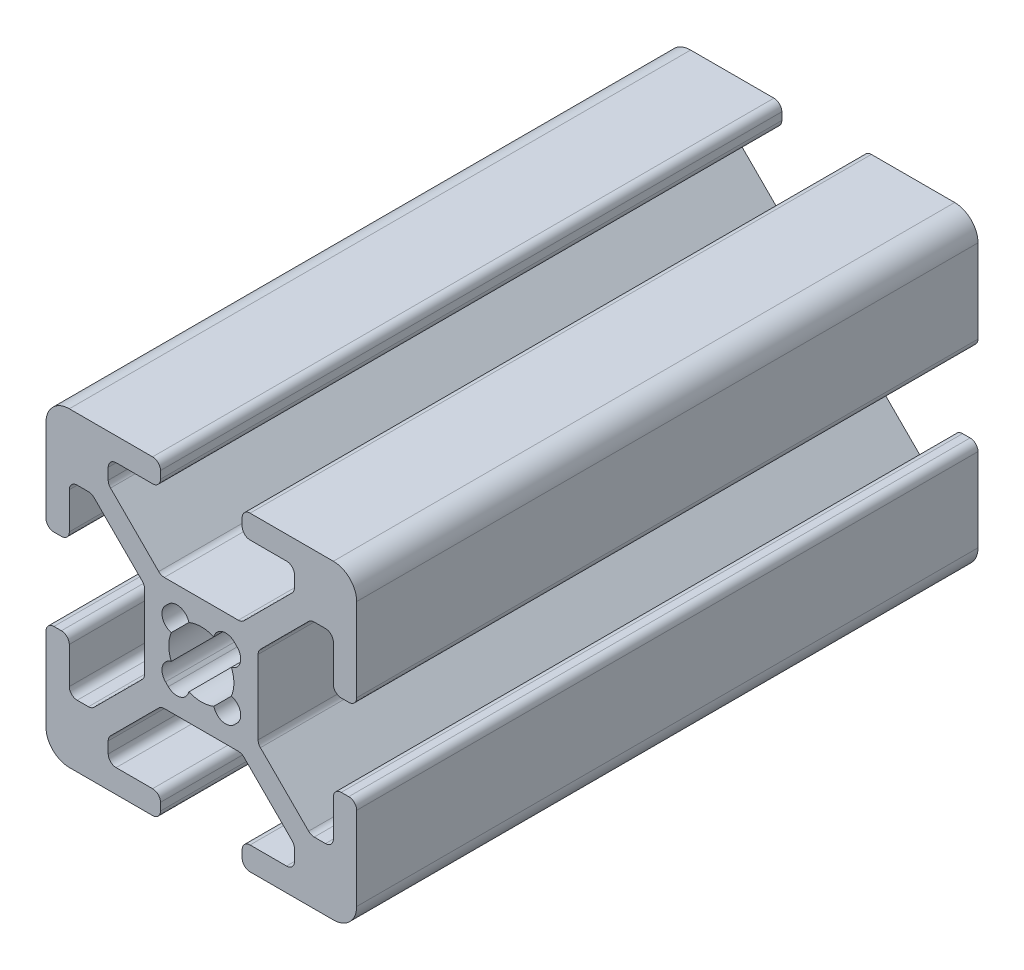
SolidWorks part; units mm, degrees
ref_plane "Front Plane" through (0, 0, 0) normal (0, 0, 1) x (1, 0, 0)
ref_plane "Top Plane" through (0, 0, 0) normal (0, 1, 0) x (1, 0, 0)
ref_plane "Right Plane" through (0, 0, 0) normal (1, 0, 0) x (0, 0, -1)
sketch "Sketch1" plane through (0, 0, 0) normal (0, 0, 1) x (1, 0, 0)
  line L0 (-5.0323, -0.3411) -> (-5.5163, -0.3411)
  line L1 (-6.0243, 0.1669) -> (-6.0243, 2.5159)
  line L2 (-4.5243, 0.1669) -> (-4.5243, 5.5289)
  line L3 (-10.8693, -5.355) -> (-10.8693, -0.5871)
  line L4 (-7.2582, 3.0239) -> (-6.5323, 3.0239)
  line L5 (-7.6174, 2.8752) -> (-10.7205, -0.2279)
  line L6 (-5.0323, -5.6011) -> (-5.5163, -5.6011)
  line L7 (-4.5243, -6.1091) -> (-4.5243, -11.4711)
  line L8 (-6.0243, -6.1091) -> (-6.0243, -8.4581)
  line L9 (-7.2582, -8.9661) -> (-6.5323, -8.9661)
  line L10 (-7.6174, -8.8173) -> (-10.7205, -5.7142)
  line L11 (-12.3994, -5.2756) -> (-12.2198, -5.096)
  line L12 (-17.1543, 6.5209) -> (-17.1543, 6.0369)
  line L13 (-17.6623, 7.0289) -> (-23.0243, 7.0289)
  line L14 (-17.6623, 5.5289) -> (-20.0113, 5.5289)
  line L15 (-12.1404, 0.6839) -> (-16.9082, 0.6839)
  line L16 (-20.5193, 4.295) -> (-20.5193, 5.0209)
  line L17 (-20.3705, 3.9358) -> (-17.2674, 0.8327)
  line L18 (-11.8943, 6.5209) -> (-11.8943, 6.0369)
  line L19 (-11.3863, 7.0289) -> (-6.0243, 7.0289)
  line L20 (-11.3863, 5.5289) -> (-9.0373, 5.5289)
  line L21 (-8.5293, 4.295) -> (-8.5293, 5.0209)
  line L22 (-8.6781, 3.9358) -> (-11.7812, 0.8327)
  line L23 (-12.2198, -0.8462) -> (-12.3994, -0.6666)
  line L24 (-24.0163, -5.6011) -> (-23.5323, -5.6011)
  line L25 (-24.5243, -6.1091) -> (-24.5243, -11.4711)
  line L26 (-23.0243, -6.1091) -> (-23.0243, -8.4581)
  line L27 (-18.1793, -0.5871) -> (-18.1793, -5.355)
  line L28 (-21.7904, -8.9661) -> (-22.5163, -8.9661)
  line L29 (-21.4312, -8.8173) -> (-18.3281, -5.7142)
  line L30 (-24.0163, -0.3411) -> (-23.5323, -0.3411)
  line L31 (-24.5243, 0.1669) -> (-24.5243, 5.5289)
  line L32 (-23.0243, 0.1669) -> (-23.0243, 2.5159)
  line L33 (-21.7904, 3.0239) -> (-22.5163, 3.0239)
  line L34 (-21.4312, 2.8752) -> (-18.3281, -0.2279)
  line L35 (-16.6492, -0.6666) -> (-16.8288, -0.8462)
  line L36 (-11.8943, -12.4631) -> (-11.8943, -11.9791)
  line L37 (-11.3863, -12.9711) -> (-6.0243, -12.9711)
  line L38 (-11.3863, -11.4711) -> (-9.0373, -11.4711)
  line L39 (-16.9082, -6.6261) -> (-12.1404, -6.6261)
  line L40 (-8.5293, -10.2371) -> (-8.5293, -10.9631)
  line L41 (-8.6781, -9.8779) -> (-11.7812, -6.7748)
  line L42 (-17.1543, -12.4631) -> (-17.1543, -11.9791)
  line L43 (-17.6623, -12.9711) -> (-23.0243, -12.9711)
  line L44 (-17.6623, -11.4711) -> (-20.0113, -11.4711)
  line L45 (-20.5193, -10.2371) -> (-20.5193, -10.9631)
  line L46 (-20.3705, -9.8779) -> (-17.2674, -6.7748)
  line L47 (-16.8288, -5.096) -> (-16.6492, -5.2756)
  arc A0 (-15.3283, -4.9062) -> (-13.7203, -4.9062) centre (-14.5243, -2.9711) ccw
  arc A1 (-6.0243, 2.5159) -> (-6.5323, 3.0239) centre (-6.5323, 2.5159) ccw
  arc A2 (-7.2582, 3.0239) -> (-7.6174, 2.8752) centre (-7.2582, 2.5159) ccw
  arc A3 (-10.7205, -0.2279) -> (-10.8693, -0.5871) centre (-10.3613, -0.5871) ccw
  arc A4 (-10.8693, -5.355) -> (-10.7205, -5.7142) centre (-10.3613, -5.355) ccw
  arc A5 (-7.6174, -8.8173) -> (-7.2582, -8.9661) centre (-7.2582, -8.4581) ccw
  arc A6 (-6.5323, -8.9661) -> (-6.0243, -8.4581) centre (-6.5323, -8.4581) ccw
  arc A7 (-5.5163, -5.6011) -> (-6.0243, -6.1091) centre (-5.5163, -6.1091) ccw
  arc A8 (-4.5243, -6.1091) -> (-5.0323, -5.6011) centre (-5.0323, -6.1091) ccw
  arc A9 (-5.0323, -0.3411) -> (-4.5243, 0.1669) centre (-5.0323, 0.1669) ccw
  arc A10 (-6.0243, 0.1669) -> (-5.5163, -0.3411) centre (-5.5163, 0.1669) ccw
  arc A11 (-13.7203, -4.9062) -> (-12.3994, -5.2756) centre (-12.9559, -4.7191) ccw
  arc A12 (-12.2198, -5.096) -> (-12.5892, -3.775) centre (-12.7763, -4.5395) ccw
  arc A13 (-17.1543, 6.5209) -> (-17.6623, 7.0289) centre (-17.6623, 6.5209) ccw
  arc A14 (-17.6623, 5.5289) -> (-17.1543, 6.0369) centre (-17.6623, 6.0369) ccw
  arc A15 (-12.5892, -3.775) -> (-12.5892, -2.1671) centre (-14.5243, -2.9711) ccw
  arc A16 (-17.2674, 0.8327) -> (-16.9082, 0.6839) centre (-16.9082, 1.1919) ccw
  arc A17 (-20.0113, 5.5289) -> (-20.5193, 5.0209) centre (-20.0113, 5.0209) ccw
  arc A18 (-20.5193, 4.295) -> (-20.3705, 3.9358) centre (-20.0113, 4.295) ccw
  arc A19 (-11.8943, 6.0369) -> (-11.3863, 5.5289) centre (-11.3863, 6.0369) ccw
  arc A20 (-11.3863, 7.0289) -> (-11.8943, 6.5209) centre (-11.3863, 6.5209) ccw
  arc A21 (-8.5293, 5.0209) -> (-9.0373, 5.5289) centre (-9.0373, 5.0209) ccw
  arc A22 (-8.6781, 3.9358) -> (-8.5293, 4.295) centre (-9.0373, 4.295) ccw
  arc A23 (-12.1404, 0.6839) -> (-11.7812, 0.8327) centre (-12.1404, 1.1919) ccw
  arc A24 (-12.5892, -2.1671) -> (-12.2198, -0.8462) centre (-12.7763, -1.4027) ccw
  arc A25 (-12.3994, -0.6666) -> (-13.7203, -1.0359) centre (-12.9559, -1.223) ccw
  arc A26 (-24.0163, -5.6011) -> (-24.5243, -6.1091) centre (-24.0163, -6.1091) ccw
  arc A27 (-23.0243, -6.1091) -> (-23.5323, -5.6011) centre (-23.5323, -6.1091) ccw
  arc A28 (-13.7203, -1.0359) -> (-15.3283, -1.0359) centre (-14.5243, -2.9711) ccw
  arc A29 (-18.3281, -5.7142) -> (-18.1793, -5.355) centre (-18.6873, -5.355) ccw
  arc A30 (-23.0243, -8.4581) -> (-22.5163, -8.9661) centre (-22.5163, -8.4581) ccw
  arc A31 (-21.7904, -8.9661) -> (-21.4312, -8.8173) centre (-21.7904, -8.4581) ccw
  arc A32 (-23.5323, -0.3411) -> (-23.0243, 0.1669) centre (-23.5323, 0.1669) ccw
  arc A33 (-24.5243, 0.1669) -> (-24.0163, -0.3411) centre (-24.0163, 0.1669) ccw
  arc A34 (-22.5163, 3.0239) -> (-23.0243, 2.5159) centre (-22.5163, 2.5159) ccw
  arc A35 (-21.4312, 2.8752) -> (-21.7904, 3.0239) centre (-21.7904, 2.5159) ccw
  arc A36 (-18.1793, -0.5871) -> (-18.3281, -0.2279) centre (-18.6873, -0.5871) ccw
  arc A37 (-15.3283, -1.0359) -> (-16.6492, -0.6666) centre (-16.0927, -1.223) ccw
  arc A38 (-16.8288, -0.8462) -> (-16.4594, -2.1671) centre (-16.2723, -1.4027) ccw
  arc A39 (-11.8943, -12.4631) -> (-11.3863, -12.9711) centre (-11.3863, -12.4631) ccw
  arc A40 (-11.3863, -11.4711) -> (-11.8943, -11.9791) centre (-11.3863, -11.9791) ccw
  arc A41 (-16.4594, -2.1671) -> (-16.4594, -3.775) centre (-14.5243, -2.9711) ccw
  arc A42 (-11.7812, -6.7748) -> (-12.1404, -6.6261) centre (-12.1404, -7.1341) ccw
  arc A43 (-9.0373, -11.4711) -> (-8.5293, -10.9631) centre (-9.0373, -10.9631) ccw
  arc A44 (-8.5293, -10.2371) -> (-8.6781, -9.8779) centre (-9.0373, -10.2371) ccw
  arc A45 (-17.1543, -11.9791) -> (-17.6623, -11.4711) centre (-17.6623, -11.9791) ccw
  arc A46 (-17.6623, -12.9711) -> (-17.1543, -12.4631) centre (-17.6623, -12.4631) ccw
  arc A47 (-20.5193, -10.9631) -> (-20.0113, -11.4711) centre (-20.0113, -10.9631) ccw
  arc A48 (-20.3705, -9.8779) -> (-20.5193, -10.2371) centre (-20.0113, -10.2371) ccw
  arc A49 (-16.9082, -6.6261) -> (-17.2674, -6.7748) centre (-16.9082, -7.1341) ccw
  arc A50 (-16.4594, -3.775) -> (-16.8288, -5.096) centre (-16.2723, -4.5395) ccw
  arc A51 (-16.6492, -5.2756) -> (-15.3283, -4.9062) centre (-16.0927, -4.7191) ccw
  arc A52 (-4.5243, 5.5289) -> (-6.0243, 7.0289) centre (-6.0243, 5.5289) ccw
  arc A53 (-6.0243, -12.9711) -> (-4.5243, -11.4711) centre (-6.0243, -11.4711) ccw
  arc A54 (-24.5243, -11.4711) -> (-23.0243, -12.9711) centre (-23.0243, -11.4711) ccw
  arc A55 (-23.0243, 7.0289) -> (-24.5243, 5.5289) centre (-23.0243, 5.5289) ccw
extrude "Extrude1" add sketch "Sketch1" along normal blind 40
